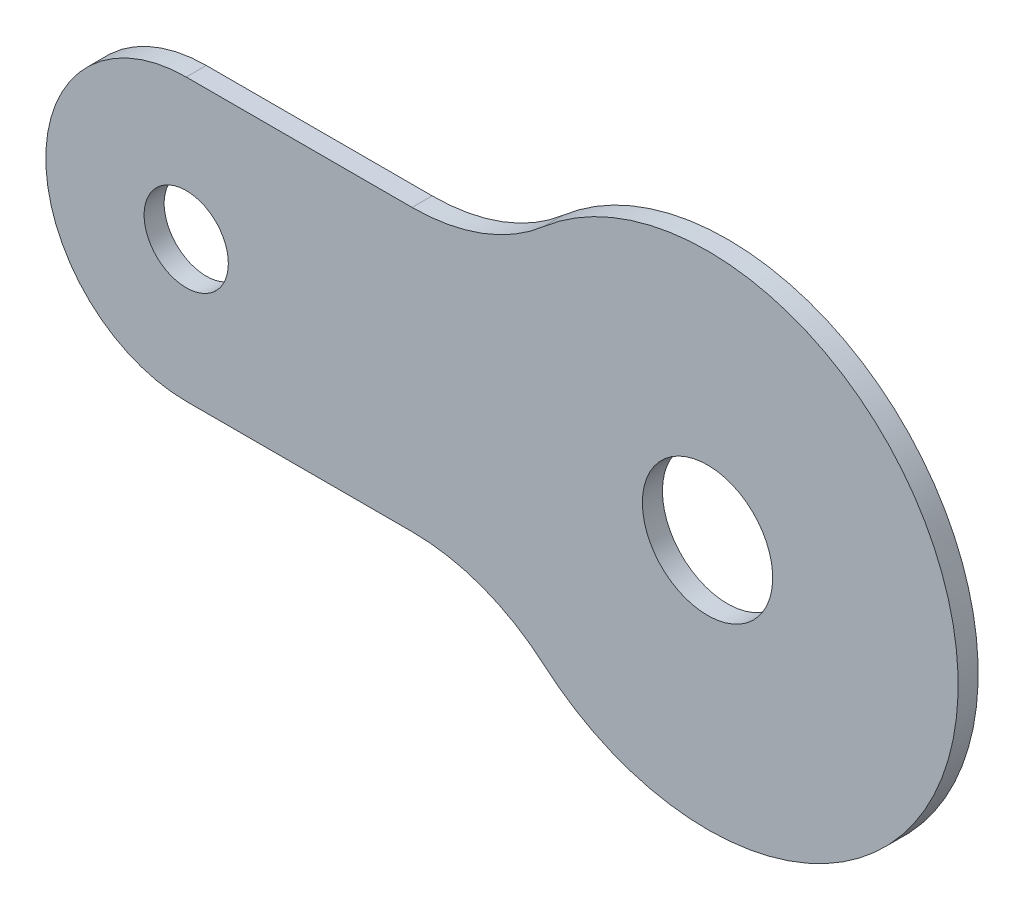
SolidWorks part; units mm, degrees
ref_plane "Plan de face" through (0, 0, 0) normal (0, 0, 1) x (1, 0, 0)
ref_plane "Plan de dessus" through (0, 0, 0) normal (0, 1, 0) x (1, 0, 0)
ref_plane "Plan de droite" through (0, 0, 0) normal (1, 0, 0) x (0, 0, -1)
sketch "Esquisse1" plane through (0, 0, 0) normal (0, 0, 1) x (1, 0, 0)
  circle A0 centre (0, 0) radius 12.5
  dimension "D1" = 25
extrude "Boss.-Extru.1" add sketch "Esquisse1" along normal blind 1
sketch "Esquisse4" plane through (0, 0, 1) normal (0, 0, 1) x (1, 0, 0)
  line L0 (0, 0) -> (-26, 0) construction
  line L1 (-26, 7.0038) -> (-10.3536, 7.0038)
  line L2 (-26, -7.0038) -> (-10.3536, -7.0038)
  circle A1 centre (0, 0) radius 12.5 construction
  circle A3 centre (0, 0) radius 12.5
  arc A4 (-10.3536, 7.0038) -> (-10.3536, -7.0038) centre (0, 0) ccw
  arc A5 (-26, 7.0038) -> (-26, -7.0038) centre (-26, 0) ccw
  dimension "D2" = 26
  dimension "D3" = 0
extrude "Boss.-Extru.2" add sketch "Esquisse4" against normal blind 1
hole_wizard "Trou pour taraudage pour trou taraudé M52" positions "Esquisse6" profile "Esquisse7" hole size "M5" standard "ISO" end condition through all
sketch "Esquisse6" plane through (0, 0, 1) normal (0, 0, 1) x (1, 0, 0)
  point P7 (-26, 0)
sketch "Esquisse7" plane through (-26, 0, 1) normal (1, 0, 0) x (0, -1, 0)
  line L0 (0, 0) -> (0, 1)
  line L1 (0, 1) -> (2.1, 1)
  line L2 (2.1, 1) -> (2.1, 0)
  line L5 (2.1, 0) -> (0, 0)
  line L11 (0, -6.35) -> (0, 107.95) construction
  dimension "Diamètre du perçage jusqu'au prochain" = 4.2
  dimension "Profondeur du perçage jusqu'au prochain" = 1
sketch "Esquisse8" plane through (0, 0, 0) normal (0, 0, -1) x (-1, 0, 0)
  circle A0 centre (0, 0) radius 3.25
  dimension "D1" = 6.5
extrude "Enlèv. mat.-Extru.1" cut sketch "Esquisse8" against normal through all
fillet "Congé1" radius 10 2 edges at (-10.3536, -7.0038, 0.5) (-10.3536, 7.0038, 0.5)
